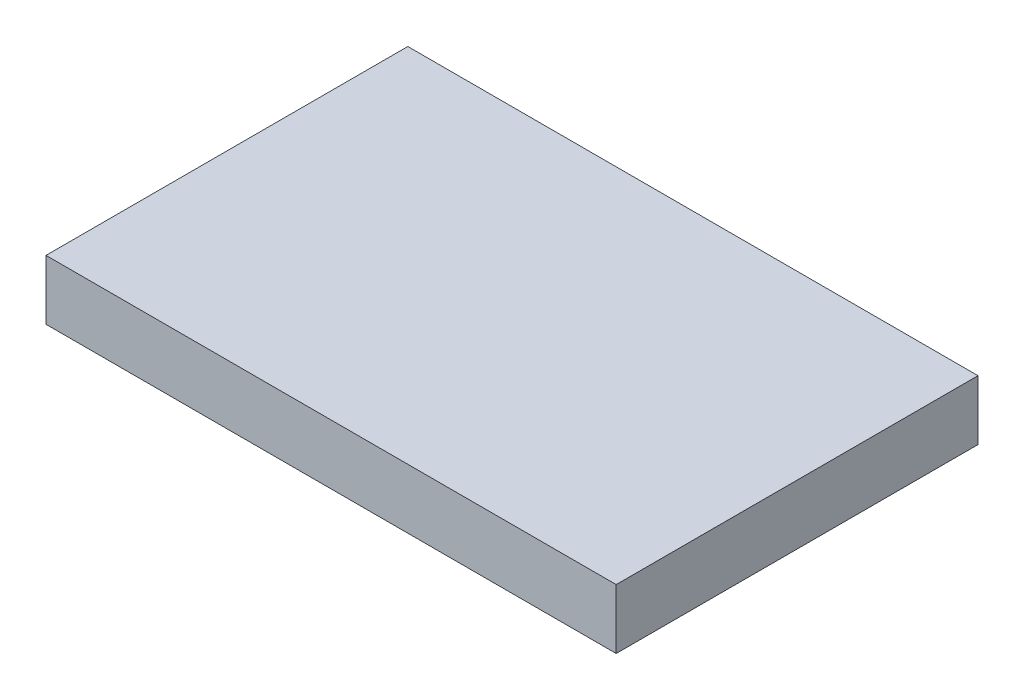
SolidWorks part; units mm, degrees
ref_plane "Alzado" through (0, 0, 0) normal (0, 0, 1) x (1, 0, 0)
ref_plane "Planta" through (0, 0, 0) normal (0, 1, 0) x (1, 0, 0)
ref_plane "Vista lateral" through (0, 0, 0) normal (1, 0, 0) x (0, 0, -1)
sketch "Croquis1" plane through (0, 0, 0) normal (0, 0, 1) x (1, 0, 0)
  line L1 (-1237.1172, 573.7168) -> (1627.8128, 573.7168)
  line L2 (-1237.1172, 573.7168) -> (-1237.1172, 273.7168)
  line L3 (-1237.1172, 273.7168) -> (1627.8128, 273.7168)
  line L4 (1627.8128, 573.7168) -> (1627.8128, 273.7168)
  dimension "D1" = 2864.93
  dimension "D2" = 300
extrude "Saliente-Extruir1" add sketch "Croquis1" along normal blind 1817.97
